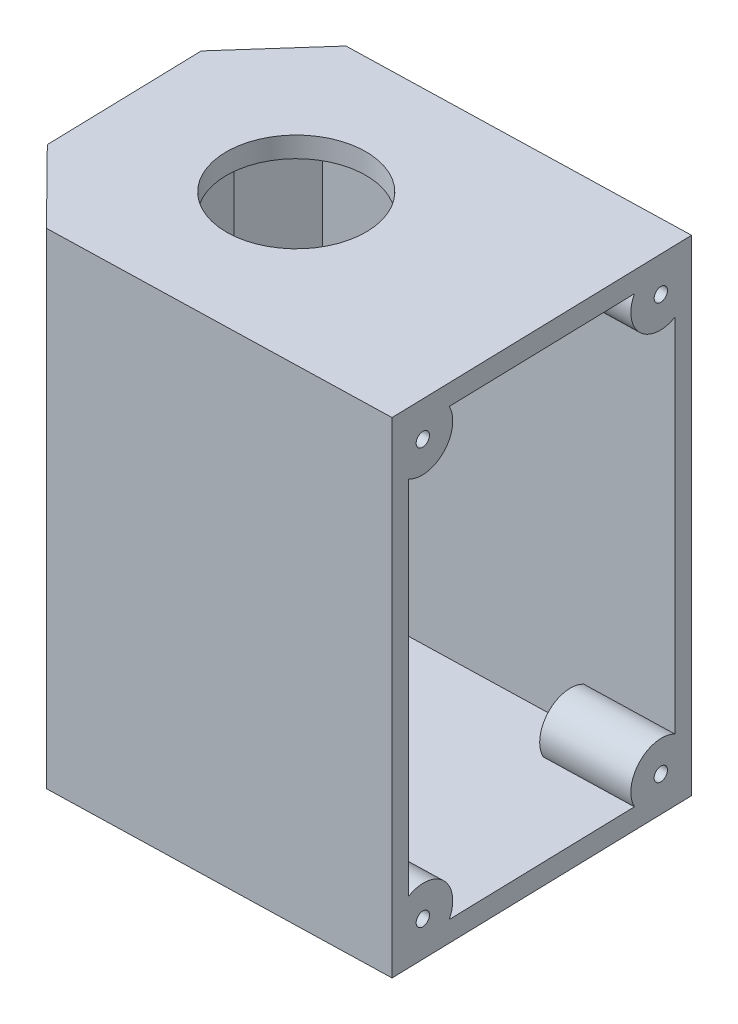
SolidWorks part; units mm, degrees
ref_plane "Front Plane" through (0, 0, 0) normal (0, 0, 1) x (1, 0, 0)
ref_plane "Top Plane" through (0, 0, 0) normal (0, 1, 0) x (1, 0, 0)
ref_plane "Right Plane" through (0, 0, 0) normal (1, 0, 0) x (0, 0, -1)
sketch "Sketch1" plane through (0, 0, 0) normal (0, 1, 0) x (1, 0, 0)
  line L0 (-17.8934, -0.436) -> (-18.4882, 22.064) construction
  line L1 (-18.4882, 22.064) -> (-17.2986, -22.936) construction
  line L2 (-17.2986, -22.936) -> (20.2014, -21.9447) construction
  line L3 (20.2014, -21.9447) -> (19.0118, 23.0553) construction
  line L4 (19.0118, 23.0553) -> (-18.4882, 22.064) construction
  line L5 (-55.9882, 21.0727) -> (19.0118, 23.0553)
  line L6 (19.0118, 23.0553) -> (20.2014, -21.9447)
  line L7 (20.2014, -21.9447) -> (-54.7986, -23.9273)
  line L8 (-55.9882, 21.0727) -> (-54.7986, -23.9273)
  circle A0 centre (-17.8934, -0.436) radius 4.9517
  dimension "D1" = 45
  dimension "D2" = 75
extrude "Boss-Extrude3" add sketch "Sketch1" along normal blind 3
sketch "Sketch4" plane through (0, 3, 0) normal (0, 1, 0) x (1, 0, 0)
  line L8 (-52.3656, -21.3621) -> (17.6362, -19.5116)
  line L9 (17.6362, -19.5116) -> (16.5787, 20.4901)
  line L10 (16.5787, 20.4901) -> (-53.423, 18.6396)
  line L11 (-53.423, 18.6396) -> (-52.3656, -21.3621)
  line L12 (-52.3656, -21.3621) -> (17.6362, -19.5116)
  line L13 (17.6362, -19.5116) -> (16.5787, 20.4901)
  line L14 (16.5787, 20.4901) -> (-53.423, 18.6396)
  line L15 (-53.423, 18.6396) -> (-52.3656, -21.3621)
  line L16 (-54.7986, -23.9273) -> (20.2014, -21.9447)
  line L17 (20.2014, -21.9447) -> (19.0118, 23.0553)
  line L18 (19.0118, 23.0553) -> (-55.9882, 21.0727)
  line L19 (-55.9882, 21.0727) -> (-54.7986, -23.9273)
  line L20 (-54.7986, -23.9273) -> (20.2014, -21.9447)
  line L21 (20.2014, -21.9447) -> (19.0118, 23.0553)
  line L22 (19.0118, 23.0553) -> (-55.9882, 21.0727)
  line L23 (-55.9882, 21.0727) -> (-54.7986, -23.9273)
  dimension "D1" = 2.5
  dimension "D2" = 0
extrude "Boss-Extrude4" add sketch "Sketch4" along normal blind 68
sketch "Sketch5" plane through (19.6076, 0, -0.5183) normal (0.9997, 0, -0.0264) x (-0.0264, 0, -0.9997)
  arc A0 (0.037, 39.9) -> (0.037, 31.1) centre (0.037, 35.5) ccw
  arc A1 (0.037, 31) -> (0.037, 40) centre (0.037, 35.5) ccw
  arc A6 (-17.463, 29.25) -> (-17.463, 25.75) centre (-17.463, 27.5) ccw
  arc A7 (-17.463, 25.75) -> (-17.463, 29.25) centre (-17.463, 27.5) ccw
  arc A8 (17.537, 25.75) -> (17.537, 29.25) centre (17.537, 27.5) ccw
  arc A9 (17.537, 29.25) -> (17.537, 25.75) centre (17.537, 27.5) ccw
  circle A10 centre (0.037, 35.5) radius 4.5
  point P0 (0.037, 35.5)
  point P33 (0.0411, 29.5)
extrude "Cut-Extrude1" cut sketch "Sketch5" against normal blind 68
sketch "Sketch10" plane through (0, 0, 0) normal (0, -1, 0) x (1, 0, 0)
  circle A0 centre (-17.8934, 0.436) radius 4.9517 construction
  circle A1 centre (-17.8934, 0.436) radius 4.9517
sketch "Sketch11" plane through (19.6076, 0, -0.5183) normal (0.9997, 0, -0.0264) x (-0.0264, 0, -0.9997)
  line L4 (-22.4709, 0) -> (22.5449, 0)
  line L5 (22.5449, 0) -> (22.5449, 71)
  line L6 (22.5449, 71) -> (-22.4709, 71)
  line L7 (-22.4709, 71) -> (-22.4709, 0)
  line L8 (-22.4709, 0) -> (22.5449, 0)
  line L9 (22.5449, 0) -> (22.5449, 71)
  line L10 (22.5449, 71) -> (-22.4709, 71)
  line L11 (-22.4709, 71) -> (-22.4709, 0)
  dimension "D1" = 0
extrude "Cut-Extrude3" cut sketch "Sketch11" against normal up to vertex (2.5 mm away)
sketch "Sketch12" plane through (0, 71, 0) normal (0, 1, 0) x (1, 0, 0)
  line L0 (-55.9882, 21.0727) -> (-54.7986, -23.9273)
  line L1 (-55.9882, 21.0727) -> (16.5127, 22.9893)
  line L2 (-54.7986, -23.9273) -> (17.7022, -22.0107)
  line L3 (16.5127, 22.9893) -> (17.7022, -22.0107)
  line L8 (-54.7986, -23.9273) -> (17.7022, -22.0107)
  line L9 (17.7022, -22.0107) -> (17.6362, -19.5116)
  line L10 (17.6362, -19.5116) -> (-52.3656, -21.3621)
  line L11 (-52.3656, -21.3621) -> (-53.423, 18.6396)
  line L12 (-53.423, 18.6396) -> (16.5787, 20.4901)
  line L13 (16.5787, 20.4901) -> (16.5127, 22.9893)
  line L14 (16.5127, 22.9893) -> (-55.9882, 21.0727)
  line L15 (-55.9882, 21.0727) -> (-54.7986, -23.9273)
  line L16 (-54.7986, -23.9273) -> (17.7022, -22.0107)
  line L17 (17.7022, -22.0107) -> (17.6362, -19.5116)
  line L18 (17.6362, -19.5116) -> (-52.3656, -21.3621)
  line L19 (-52.3656, -21.3621) -> (-53.423, 18.6396)
  line L20 (-53.423, 18.6396) -> (16.5787, 20.4901)
  line L21 (16.5787, 20.4901) -> (16.5127, 22.9893)
  line L22 (16.5127, 22.9893) -> (-55.9882, 21.0727)
  line L23 (-55.9882, 21.0727) -> (-54.7986, -23.9273)
  circle A0 centre (-17.8934, -0.436) radius 13
  line M11 (17.6362, -19.5116) -> (-52.3656, -21.3621)
  line M12 (-52.3656, -21.3621) -> (-53.423, 18.6396)
  line M13 (-53.423, 18.6396) -> (16.5787, 20.4901)
  dimension "D2" = 26
  dimension "D1" = 0
extrude "Boss-Extrude7" add sketch "Sketch12" against normal blind 3 contours L3 A0 M13 M12 M11
sketch "Sketch13" plane through (-55.3924, 0, 1.4643) normal (-0.9997, 0, 0.0264) x (0.0264, 0, 0.9997)
  line L4 (-22.5449, 0) -> (22.4709, 0)
  line L5 (22.4709, 0) -> (22.4709, 71)
  line L6 (22.4709, 71) -> (-22.5449, 71)
  line L7 (-22.5449, 71) -> (-22.5449, 0)
  line L8 (-22.5449, 0) -> (22.4709, 0)
  line L9 (22.4709, 0) -> (22.4709, 71)
  line L10 (22.4709, 71) -> (-22.5449, 71)
  line L11 (-22.5449, 71) -> (-22.5449, 0)
  dimension "D1" = 0
extrude "Cut-Extrude4" cut sketch "Sketch13" against normal blind 13
sketch "Sketch14" plane through (-42.397, 0, 1.1208) normal (-0.9997, 0, 0.0264) x (0.0264, 0, 0.9997)
  line L4 (-22.5449, 71) -> (-22.5449, 0)
  line L5 (-22.5449, 0) -> (22.4709, 0)
  line L6 (22.4709, 0) -> (22.4709, 71)
  line L7 (22.4709, 71) -> (-22.5449, 71)
  line L8 (-22.5449, 71) -> (-22.5449, 0)
  line L9 (-22.5449, 0) -> (22.4709, 0)
  line L10 (22.4709, 0) -> (22.4709, 71)
  line L11 (22.4709, 71) -> (-22.5449, 71)
  dimension "D1" = 0
extrude "Boss-Extrude8" add sketch "Sketch14" against normal blind 3
sketch "Sketch15" plane through (17.1084, 0, -0.4523) normal (0.9997, 0, -0.0264) x (-0.0264, 0, -0.9997)
  line L0 (-19.9709, 3) -> (-19.9709, 68) construction
  line L1 (0.037, 71) -> (0.037, -4.943) construction
  line L3 (-22.4709, 35.5) -> (22.5449, 35.5) construction
  line L4 (-22.4709, 71) -> (-22.4709, 0) construction
  line L5 (22.5449, 0) -> (22.5449, 71) construction
  line L7 (-19.9709, 3) -> (-19.9709, 35.5)
  line L8 (22.5449, 71) -> (-22.4709, 71) construction
  line L9 (-19.9709, 61.9101) -> (-19.9709, 68)
  line L10 (-13.8809, 68) -> (-19.9709, 68)
  line L15 (-13.8809, 3) -> (-19.9709, 3)
  line L16 (-19.9709, 9.0899) -> (-19.9709, 3)
  line L17 (20.0449, 9.0899) -> (20.0449, 3)
  line L18 (13.9549, 3) -> (20.0449, 3)
  line L19 (13.9549, 68) -> (20.0449, 68)
  line L20 (20.0449, 61.9101) -> (20.0449, 68)
  line L21 (20.0449, 3) -> (20.0449, 35.5)
  circle A0 centre (-17.8495, 65.8787) radius 1.5
  circle A3 centre (-17.8495, 5.1213) radius 1.5
  arc A4 (-19.9709, 61.9101) -> (-13.8809, 68) centre (-17.8495, 65.8787) ccw
  circle A5 centre (-17.8495, 65.8787) radius 4.5 construction
  arc A10 (-19.9709, 9.0899) -> (-13.8809, 3) centre (-17.8495, 5.1213) cw
  circle A12 centre (-17.8495, 5.1213) radius 1.5
  circle A13 centre (17.9235, 5.1213) radius 1.5
  arc A14 (20.0449, 9.0899) -> (13.9549, 3) centre (17.9235, 5.1213) ccw
  arc A15 (20.0449, 61.9101) -> (13.9549, 68) centre (17.9235, 65.8787) cw
  circle A16 centre (17.9235, 5.1213) radius 1.5
  circle A17 centre (17.9235, 65.8787) radius 1.5
  line M7 (-19.9709, 3) -> (-19.9709, 68)
  line M8 (-19.9709, 68) -> (20.0449, 68)
  line M9 (20.0449, 68) -> (20.0449, 3)
  line M10 (20.0449, 3) -> (-19.9709, 3)
  dimension "D2" = 3
  dimension "D1" = 3
extrude "Boss-Extrude11" add sketch "Sketch15" against normal up to surface (56.5262 mm away) contours A14 A13 M9 M10 | A10 A3 M7 M10 | A15 A17 M9 M8 | A4 A0 M7 M8 up to face at (-39.399, 35.5, 1.0045)
sketch "Sketch16" plane through (0, 3, 0) normal (0, 1, 0) x (1, 0, 0)
  circle A0 centre (-17.8934, -0.436) radius 4.15
  circle A2 centre (-17.8934, -0.436) radius 9
  dimension "D1" = 8.3
  dimension "D2" = 18
extrude "Boss-Extrude12" add sketch "Sketch16" along normal blind 2 and the other way up to surface other way up to face at (-12.6453, 0, 0.2973)
sketch "Sketch17" plane through (0, 5, 0) normal (0, 1, 0) x (1, 0, 0)
  circle A0 centre (-17.8934, -0.436) radius 1
  circle A2 centre (-17.8934, -0.436) radius 9
  circle A3 centre (-17.8934, -0.436) radius 9
  dimension "D1" = 2
  dimension "D2" = 0
extrude "Boss-Extrude13" add sketch "Sketch17" along normal blind 2
sketch "Sketch18" plane through (0, 71, 0) normal (0, 1, 0) x (1, 0, 0)
  circle A0 centre (-17.8934, -0.436) radius 1 construction
  circle A1 centre (-17.8934, -0.436) radius 1
  circle A2 centre (-17.8934, -0.436) radius 13 construction
  circle A3 centre (-17.8934, -0.436) radius 13
extrude "Boss-Extrude14" add sketch "Sketch18" against normal up to surface (3 mm away) up to face at (-17.8934, 68, 13.436)
sketch "Sketch19" plane through (17.1084, 0, -0.4523) normal (0.9997, 0, -0.0264) x (-0.0264, 0, -0.9997)
  circle A0 centre (-17.8495, 5.1213) radius 1.5 construction
  circle A1 centre (17.9235, 5.1213) radius 1.5 construction
  circle A2 centre (-17.8495, 65.8787) radius 1.5 construction
  circle A3 centre (17.9235, 65.8787) radius 1.5 construction
  circle A4 centre (-17.8495, 5.1213) radius 1.5
  circle A5 centre (17.9235, 5.1213) radius 1.5
  circle A6 centre (-17.8495, 65.8787) radius 1.5
  circle A7 centre (17.9235, 65.8787) radius 1.5
  circle A8 centre (-17.8495, 65.8787) radius 1
  circle A9 centre (17.9235, 65.8787) radius 1
  circle A10 centre (17.9235, 5.1213) radius 1
  circle A11 centre (-17.8495, 5.1213) radius 1
  dimension "D1" = 2
extrude "Boss-Extrude15" add sketch "Sketch19" against normal up to surface (56.5262 mm away) up to face at (-39.399, 35.5, 1.0045)
ref_plane "Plane1" through (4.113, 0, -0.1087) normal (0.9997, 0, -0.0264) x (-0.0264, 0, -0.9997)
sketch "Sketch23" plane through (4.113, 0, -0.1087) normal (0.9997, 0, -0.0264) x (-0.0264, 0, -0.9997)
  line L0 (-19.9709, 9.0899) -> (-19.9709, 68)
  line L1 (-19.9709, 9.0899) -> (-19.9709, 3)
  line L2 (-13.8809, 3) -> (20.0449, 3)
  line L3 (20.0449, 9.0899) -> (20.0449, 68)
  line L4 (20.0449, 68) -> (20.0449, 3)
  line L5 (3.5262, 3) -> (-19.9709, 3)
  line L6 (-13.8809, 68) -> (20.0449, 68)
  line L7 (20.0449, 68) -> (-19.9709, 68)
  line L8 (9.037, 7) -> (-8.963, 7) construction
  line L9 (9.037, 7) -> (-8.963, 7)
  line L10 (9.037, 3) -> (-8.963, 3) construction
  line L11 (9.037, 3) -> (-8.963, 3)
  line L12 (-8.963, 7) -> (-8.963, 3)
  line L13 (9.037, 7) -> (9.037, 3)
extrude "Cut-Extrude9" cut sketch "Sketch23" against normal up to surface (43.5262 mm away) contours L9 L13 L2 L4 L3 L6 L7 L0 L1 L5 L12 up to face at (-39.399, 35.5, 1.0045)
sketch "Sketch27" plane through (0, 71, 0) normal (0, 1, 0) x (1, 0, 0)
  circle A0 centre (-17.8934, -0.436) radius 1 construction
  circle A1 centre (-17.8934, -0.436) radius 1
  circle A2 centre (-17.8934, -0.436) radius 10
  dimension "D1" = 20
extrude "Cut-Extrude12" cut sketch "Sketch27" against normal blind 10
sketch "Sketch28" plane through (0, 0, 0) normal (0, -1, 0) x (1, 0, 0)
  circle A1 centre (-17.8934, 0.436) radius 4.15
  circle A2 centre (-17.8934, 0.436) radius 4.15
  dimension "D1" = 0
extrude "Cut-Extrude13" cut sketch "Sketch28" against normal blind 73
sketch "Sketch29" plane through (0, 0, 0) normal (0, -1, 0) x (1, 0, 0)
  circle A0 centre (-17.8934, 0.436) radius 4.15 construction
  circle A1 centre (-17.8934, 0.436) radius 4.15
  circle A2 centre (-17.8934, 0.436) radius 4.5
  dimension "D1" = 9
extrude "Cut-Extrude14" cut sketch "Sketch29" against normal blind 73
sketch "Sketch30" plane through (0, 7, 0) normal (0, 1, 0) x (1, 0, 0)
  circle A1 centre (-17.8934, -0.436) radius 9
  circle A2 centre (-17.8934, -0.436) radius 9
  dimension "D1" = 0
extrude "Cut-Extrude15" cut sketch "Sketch30" against normal up to surface (4 mm away) up to face at (-3.5169, 3, 0.056)
sketch "Sketch31" plane through (0, 71, 0) normal (0, 1, 0) x (1, 0, 0)
  circle A2 centre (-17.8934, -0.436) radius 10.2
  circle A3 centre (-17.8934, -0.436) radius 10.2
  dimension "D1" = 0.2
extrude "Cut-Extrude17" cut sketch "Sketch31" against normal up to surface (3 mm away) up to face at (-17.8934, 68, 10.436)
sketch "Sketch32" plane through (0, 71, 0) normal (0, 1, 0) x (1, 0, 0)
  line L1 (-42.7037, 10.481) -> (-32.7442, 21.6871)
  line L2 (16.5127, 22.9893) -> (-42.9928, 21.4162) construction
  line L3 (-42.398, -1.0838) -> (-29.4389, -0.7412) construction
  line L4 (-42.0922, -12.6485) -> (-31.5546, -23.3129)
  line L7 (-41.8032, -23.5838) -> (17.7022, -22.0107)
  line L8 (17.7022, -22.0107) -> (16.5127, 22.9893)
  line L9 (16.5127, 22.9893) -> (-42.9928, 21.4162)
  line L10 (-42.9928, 21.4162) -> (-41.8032, -23.5838)
  line L11 (-41.8032, -23.5838) -> (17.7022, -22.0107)
  line L12 (17.7022, -22.0107) -> (16.5127, 22.9893)
  line L13 (16.5127, 22.9893) -> (-42.9928, 21.4162)
  line L14 (-42.9928, 21.4162) -> (-41.8032, -23.5838)
  point P8 (-37.7239, 16.084)
  point P17 (-36.8234, -17.9807)
  line M7 (-41.8032, -23.5838) -> (17.7022, -22.0107)
  line M9 (16.5127, 22.9893) -> (-42.9928, 21.4162)
  line M10 (-42.9928, 21.4162) -> (-41.8032, -23.5838)
  dimension "D1" = 0
extrude "Cut-Extrude18" cut sketch "Sketch32" against normal blind 197 contours L1 M10 M9 | L4 M10 M7
sketch "Sketch33" plane through (-27.6214, 0, 27.2933) normal (-0.7113, 0, 0.7029) x (0.7029, 0, 0.7113)
  line L4 (-20.5883, 0) -> (-5.5959, 0)
  line L5 (-5.5959, 0) -> (-5.5959, 71)
  line L6 (-5.5959, 71) -> (-20.5883, 71)
  line L7 (-20.5883, 71) -> (-20.5883, 0)
  line L8 (-20.5883, 0) -> (-5.5959, 0)
  line L9 (-5.5959, 0) -> (-5.5959, 71)
  line L10 (-5.5959, 71) -> (-20.5883, 71)
  line L11 (-20.5883, 71) -> (-20.5883, 0)
  dimension "D1" = 0
extrude "Boss-Extrude16" add sketch "Sketch33" against normal blind 1
sketch "Sketch34" plane through (-29.0626, 0, -25.8295) normal (-0.7475, 0, -0.6643) x (-0.6643, 0, 0.7475)
  line L4 (20.5343, 0) -> (20.5343, 71)
  line L5 (20.5343, 71) -> (5.5419, 71)
  line L6 (5.5419, 71) -> (5.5419, 0)
  line L7 (5.5419, 0) -> (20.5343, 0)
  line L8 (20.5343, 0) -> (20.5343, 71)
  line L9 (20.5343, 71) -> (5.5419, 71)
  line L10 (5.5419, 71) -> (5.5419, 0)
  line L11 (5.5419, 0) -> (20.5343, 0)
  dimension "D1" = 0
extrude "Boss-Extrude17" add sketch "Sketch34" against normal blind 1
